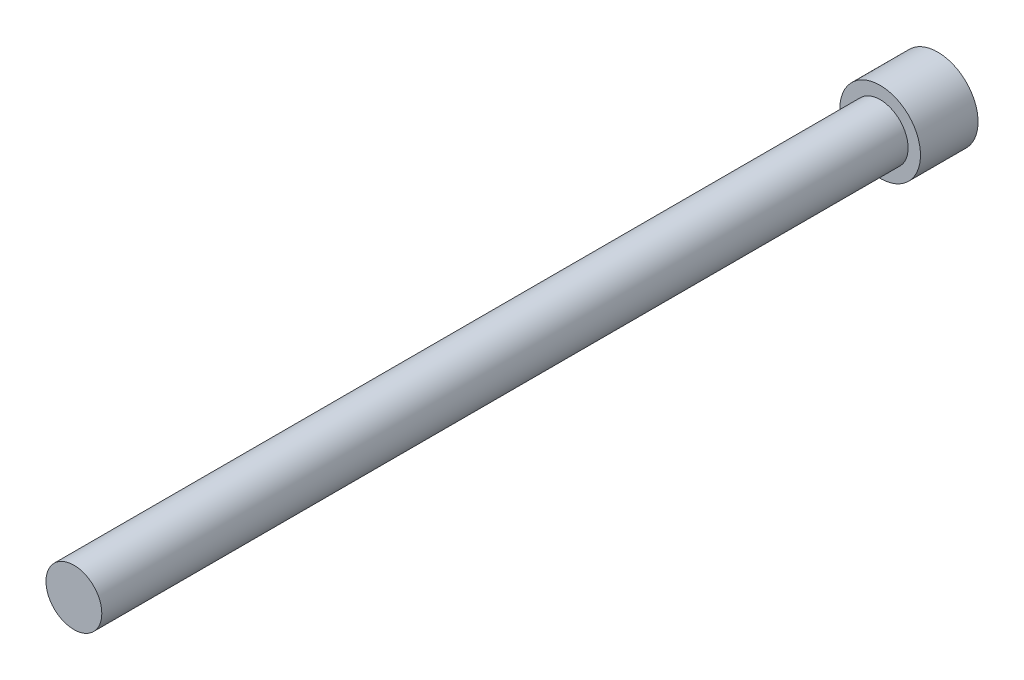
SolidWorks part; units mm, degrees
ref_plane "Alzado" through (0, 0, 0) normal (0, 0, 1) x (1, 0, 0)
ref_plane "Planta" through (0, 0, 0) normal (0, 1, 0) x (1, 0, 0)
ref_plane "Vista lateral" through (0, 0, 0) normal (1, 0, 0) x (0, 0, -1)
sketch "Croquis1" plane through (0, 0, 0) normal (0, 0, 1) x (1, 0, 0)
  circle A0 centre (0, 0) radius 2.425
  dimension "D1" = 4.85
extrude "Saliente-Extruir1" add sketch "Croquis1" along normal blind 70
sketch "Croquis2" plane through (0, 0, 0) normal (0, 0, -1) x (-1, 0, 0)
  circle A0 centre (0, 0) radius 3.5
  dimension "D1" = 7
extrude "Saliente-Extruir2" add sketch "Croquis2" along normal blind 5
